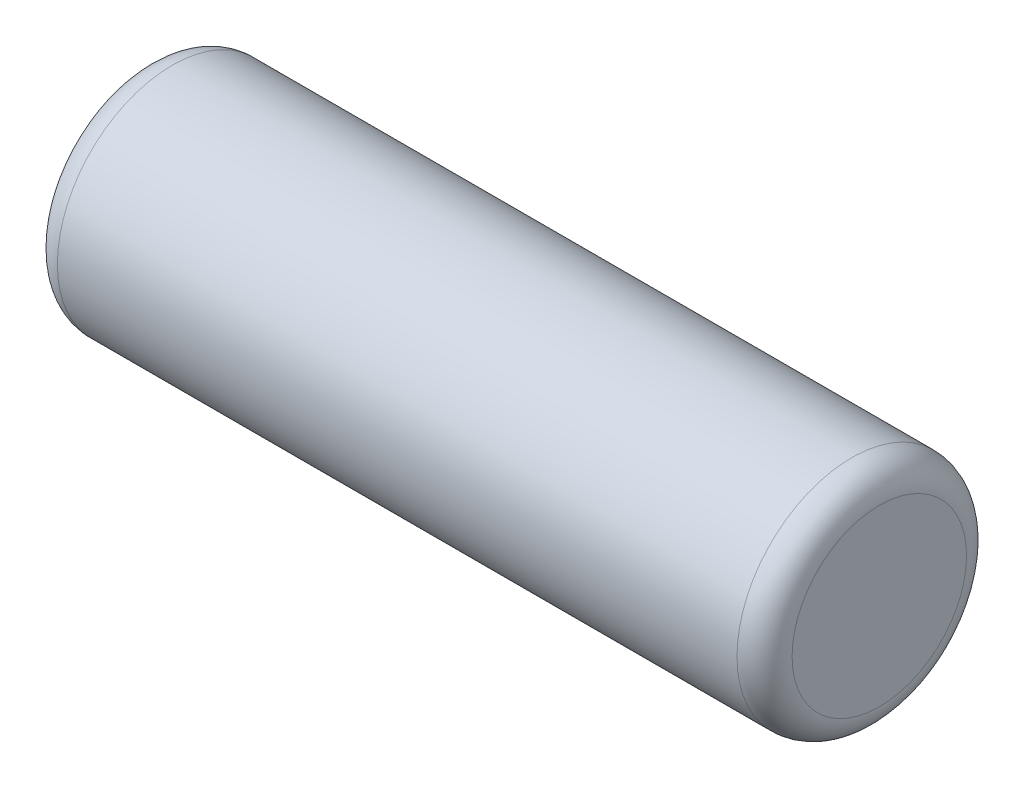
SolidWorks part; units mm, degrees
ref_plane "Face" through (0, 0, 0) normal (0, 0, 1) x (1, 0, 0)
ref_plane "Dessus" through (0, 0, 0) normal (0, 1, 0) x (1, 0, 0)
ref_plane "Droite" through (0, 0, 0) normal (1, 0, 0) x (0, 0, -1)
sketch "Esquisse1" plane through (0, 0, 0) normal (0, 0, 1) x (1, 0, 0)
  line L0 (-17, 0) -> (33, 0) construction
  line L2 (-4, 0) -> (4, 0)
  line L3 (-4, 0) -> (-4, 1.25)
  line L4 (-4, 1.25) -> (4, 1.25)
  line L5 (4, 0) -> (4, 1.25)
  dimension "Longueur" = 8
  dimension "Diamètre" = 2.5
revolve "Base-Révolution" add sketch "Esquisse1" angle 360 about L0
fillet "Congé1" radius 0.3
